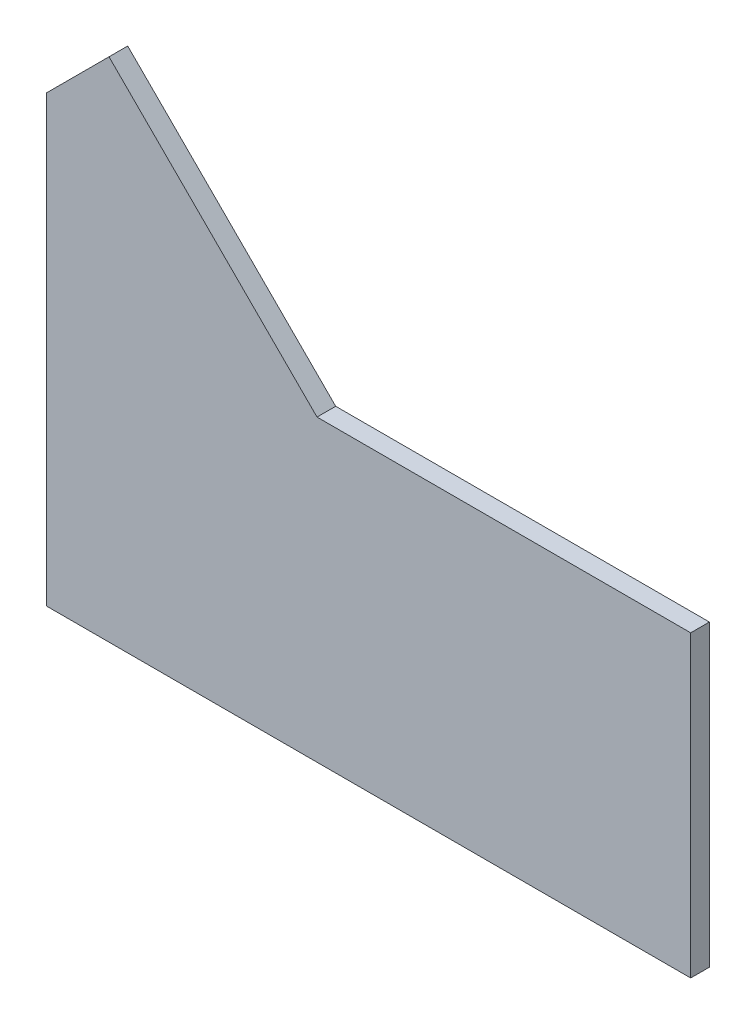
SolidWorks part; units mm, degrees
ref_plane "Front Plane" through (0, 0, 0) normal (0, 0, 1) x (1, 0, 0)
ref_plane "Top Plane" through (0, 0, 0) normal (0, 1, 0) x (1, 0, 0)
ref_plane "Right Plane" through (0, 0, 0) normal (1, 0, 0) x (0, 0, -1)
sketch "Sketch1" plane through (0, 0, 0) normal (0, 0, 1) x (1, 0, 0)
  line L0 (0, 0) -> (127, 0)
  line L1 (127, 0) -> (127, 101.6)
  line L3 (0, 101.6) -> (0, 0) construction
  line L4 (0, 101.6) -> (-70.6924, 172.2924)
  line L5 (-70.6924, 172.2924) -> (-91.8969, 151.088)
  line L6 (-91.8969, 151.088) -> (-91.8969, 0)
  line L7 (-91.8969, 0) -> (0, 0)
  line L8 (127, 101.6) -> (0, 101.6)
  dimension "D1" = 127
  dimension "D2" = 101.6
  dimension "D3" = 135
  dimension "D4" = 29.9876
  dimension "D5" = 151.088
extrude "Boss-Extrude1" add sketch "Sketch1" along normal blind 6.35
sketch "Sketch2" plane through (0, 0, 0) normal (0, 0, -1) x (-1, 0, 0)
  line L0 (0, 101.6) -> (-12.7, 101.6) construction
  line L1 (-127, 101.6) -> (0, 101.6) construction
  line L2 (-12.7, 101.6) -> (-44.577, 101.6)
  line L3 (-12.7, 101.6) -> (-48.621, 65.679)
  line L4 (-44.577, 101.6) -> (-80.498, 65.679)
  line L5 (-80.498, 65.679) -> (-48.621, 65.679)
  line L6 (-62.5375, 83.6395) -> (-30.6605, 83.6395) construction
  line L7 (-44.577, 101.6) -> (-62.5375, 83.6395)
  circle A0 centre (-46.599, 83.6395) radius 11.049
  dimension "D9" = 22.098
  dimension "D1" = 12.7
  dimension "D2" = 31.877
  dimension "D3" = 50.8
  dimension "D4" = 45
  dimension "D5" = 45
  dimension "D6" = 50.8
  dimension "D7" = 135
  dimension "D8" = 25.4
sketch "Sketch3" plane through (0, 0, 0) normal (0, 0, -1) x (-1, 0, 0)
  line L0 (70.6924, 172.2924) -> (61.7122, 163.3122) construction
  line L1 (0, 101.6) -> (70.6924, 172.2924) construction
  line L2 (59.4671, 161.0671) -> (63.9572, 165.5572)
  line L3 (59.4671, 161.0671) -> (63.9572, 156.577) construction
  line L5 (68.4474, 161.0671) -> (63.9572, 165.5572) construction
  line L6 (70.6924, 172.2924) -> (91.8969, 151.088) construction
  line L7 (63.9572, 156.577) -> (68.4474, 161.0671)
  line L8 (63.9572, 156.577) -> (66.2023, 154.3319)
  line L9 (68.4474, 161.0671) -> (70.6924, 158.822)
  line L10 (70.6924, 158.822) -> (66.2023, 154.3319)
  line L11 (-127, 25.4) -> (-127, 0)
  line L12 (-127, 50.8) -> (-127, 101.6) construction
  line L13 (-127, 0) -> (-127, 50.8) construction
  line L14 (-38.1, 101.6) -> (-25.4, 101.6)
  line L15 (-127, 82.55) -> (-127, 69.85)
  line L16 (0, 101.6) -> (-63.5, 101.6) construction
  line L17 (-127, 44.45) -> (-127, 57.15)
  line L18 (-127, 19.05) -> (-127, 31.75)
  line L19 (-63.5, 101.6) -> (-127, 101.6) construction
  line L20 (-101.6, 101.6) -> (-88.9, 101.6)
  line L21 (-69.85, 101.6) -> (-57.15, 101.6)
  line L22 (70.6924, 172.2924) -> (0, 101.6) construction
  line L23 (30.8561, 132.4561) -> (39.8363, 141.4363)
  line L24 (91.8969, 119.666) -> (91.8969, 106.966)
  line L25 (91.8969, 0) -> (91.8969, 75.544) construction
  line L26 (91.8969, 75.544) -> (91.8969, 151.088) construction
  line L27 (91.8969, 81.894) -> (91.8969, 69.194)
  line L28 (91.8969, 44.122) -> (91.8969, 31.422)
  line L29 (30.8561, 132.4561) -> (33.1011, 130.211)
  line L30 (-127, 82.55) -> (-123.825, 82.55)
  line L31 (-127, 82.55) -> (-127, 69.85)
  line L32 (-127, 69.85) -> (-123.825, 69.85)
  line L33 (-123.825, 82.55) -> (-123.825, 69.85)
  line L34 (-127, 57.15) -> (-123.825, 57.15)
  line L35 (-127, 57.15) -> (-127, 44.45)
  line L36 (-127, 44.45) -> (-123.825, 44.45)
  line L37 (-123.825, 57.15) -> (-123.825, 44.45)
  line L38 (-127, 31.75) -> (-123.825, 31.75)
  line L39 (-127, 31.75) -> (-127, 19.05)
  line L40 (-127, 19.05) -> (-123.825, 19.05)
  line L41 (-123.825, 31.75) -> (-123.825, 19.05)
  line L42 (-101.6, 101.6) -> (-88.9, 101.6)
  line L43 (-101.6, 101.6) -> (-101.6, 98.425)
  line L44 (-101.6, 98.425) -> (-88.9, 98.425)
  line L45 (-88.9, 101.6) -> (-88.9, 98.425)
  line L46 (-69.85, 101.6) -> (-57.15, 101.6)
  line L47 (-69.85, 101.6) -> (-69.85, 98.425)
  line L48 (-69.85, 98.425) -> (-57.15, 98.425)
  line L49 (-57.15, 101.6) -> (-57.15, 98.425)
  line L50 (-25.4, 101.6) -> (-38.1, 101.6)
  line L51 (-25.4, 101.6) -> (-25.4, 98.425)
  line L52 (-25.4, 98.425) -> (-38.1, 98.425)
  line L53 (-38.1, 101.6) -> (-38.1, 98.425)
  line L54 (39.8363, 141.4363) -> (42.0814, 139.1913)
  line L55 (42.0814, 139.1913) -> (33.1011, 130.211)
  line L56 (-123.825, 77.4827) -> (-123.825, 74.9173)
  line L57 (91.8969, 119.666) -> (88.7219, 119.666)
  line L58 (91.8969, 119.666) -> (91.8969, 106.966)
  line L59 (91.8969, 106.966) -> (88.7219, 106.966)
  line L60 (88.7219, 119.666) -> (88.7219, 106.966)
  line L61 (91.8969, 81.894) -> (88.7219, 81.894)
  line L62 (91.8969, 81.894) -> (91.8969, 69.194)
  line L63 (91.8969, 69.194) -> (88.7219, 69.194)
  line L64 (88.7219, 81.894) -> (88.7219, 69.194)
  line L65 (91.8969, 44.122) -> (88.7219, 44.122)
  line L66 (91.8969, 44.122) -> (91.8969, 31.422)
  line L67 (91.8969, 31.422) -> (88.7219, 31.422)
  line L68 (88.7219, 44.122) -> (88.7219, 31.422)
  line L70 (-123.825, 77.4827) -> (-111.125, 77.4827)
  line L71 (-123.825, 77.4827) -> (-123.825, 74.9173)
  line L72 (-123.825, 74.9173) -> (-111.125, 74.9173)
  line L73 (-111.125, 77.4827) -> (-111.125, 74.9173)
  point P8 (61.7122, 163.3122)
  point P27 (-127, 76.2)
  point P30 (-127, 50.8)
  point P33 (-127, 25.4)
  point P34 (-95.25, 101.6)
  point P36 (-95.25, 101.6)
  point P41 (-31.75, 101.6)
  point P42 (-63.5, 101.6)
  point P45 (35.3462, 136.9462)
  point P53 (91.8969, 113.316)
  point P56 (91.8969, 75.544)
  point P59 (91.8969, 37.772)
  point P82 (-123.825, 76.2)
  dimension "D1" = 12.7
  dimension "D2" = 9.525
  dimension "D3" = 6.35
  dimension "D4" = 6.35
  dimension "D5" = 6.35
  dimension "D6" = 3.175
  dimension "D7" = 3.175
  dimension "D8" = 12.7
  dimension "D9" = 12.7
  dimension "D10" = 12.7
  dimension "D11" = 25.4
  dimension "D12" = 12.7
  dimension "D13" = 12.7
  dimension "D14" = 12.7
  dimension "D15" = 31.75
  dimension "D16" = 12.7
  dimension "D17" = 75.544
  dimension "D18" = 12.7
  dimension "D19" = 12.7
  dimension "D20" = 12.7
  dimension "D21" = 3.175
  dimension "D22" = 3.175
  dimension "D23" = 3.175
  dimension "D24" = 3.175
  dimension "D25" = 3.175
  dimension "D26" = 3.175
  dimension "D27" = 3.175
  dimension "D28" = 3.175
  dimension "D29" = 12.7
  dimension "D30" = 3.175
  dimension "D31" = 3.175
  dimension "D32" = 3.175
  dimension "D33" = 2.5654
  dimension "D34" = 12.7
